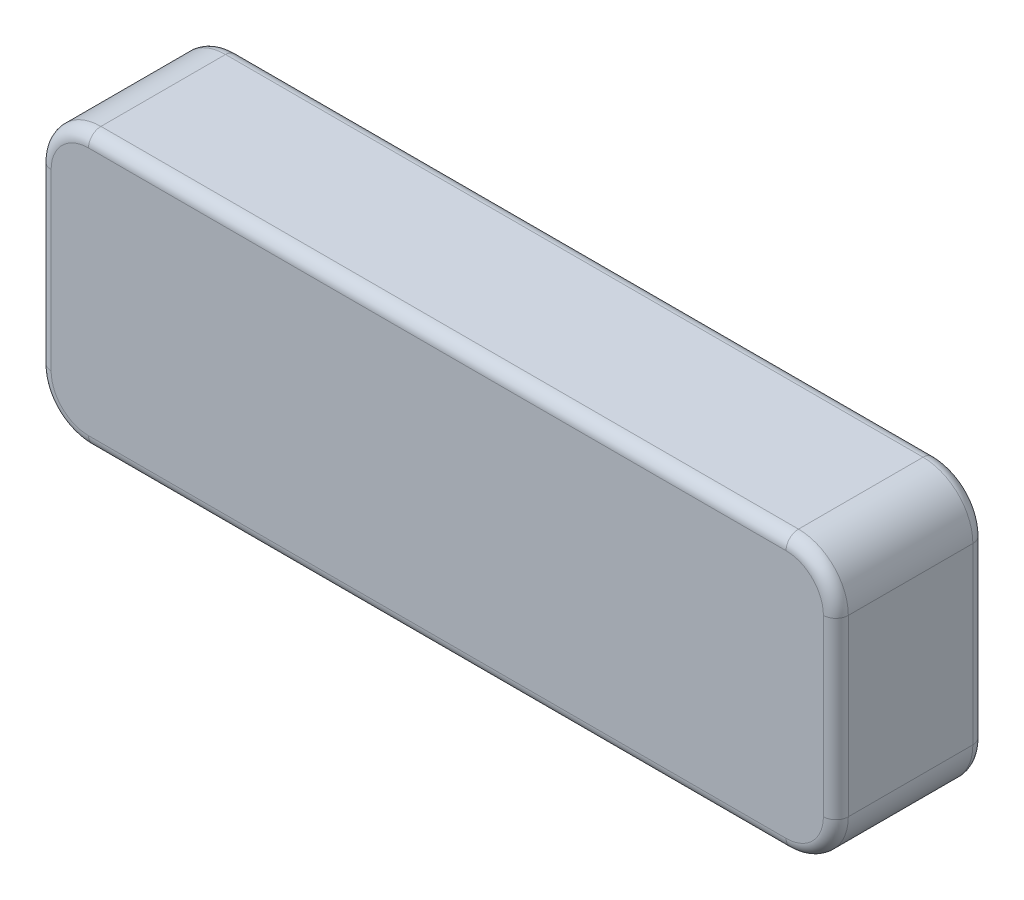
SolidWorks part; units mm, degrees
ref_plane "Front Plane" through (0, 0, 0) normal (0, 0, 1) x (1, 0, 0)
ref_plane "Top Plane" through (0, 0, 0) normal (0, 1, 0) x (1, 0, 0)
ref_plane "Right Plane" through (0, 0, 0) normal (1, 0, 0) x (0, 0, -1)
sketch "Sketch1" plane through (0, 0, 0) normal (0, 0, 1) x (1, 0, 0)
  line L1 (-203.2, -69.85) -> (203.2, -69.85)
  line L2 (-203.2, -69.85) -> (-203.2, 69.85)
  line L3 (-203.2, 69.85) -> (203.2, 69.85)
  line L4 (203.2, -69.85) -> (203.2, 69.85)
  line L5 (-203.2, -69.85) -> (203.2, 69.85) construction
  line L6 (-203.2, 69.85) -> (203.2, -69.85) construction
  point P0 (0, 0)
  dimension "D1" = 406.4
  dimension "D2" = 139.7
extrude "Boss-Extrude1" add sketch "Sketch1" along normal blind 76.2
fillet "Fillet1" radius 25.4 4 edges at (203.2, -69.85, 38.1) (-203.2, -69.85, 38.1) (-203.2, 69.85, 38.1) (203.2, 69.85, 38.1)
fillet "Fillet2" radius 6.35 16 edges at (195.7605, 62.4105, 0) (203.2, 0, 0) (195.7605, -62.4105, 0) (0, -69.85, 0) (-195.7605, -62.4105, 0) (-203.2, 0, 0) (-195.7605, 62.4105, 0) (195.7605, 62.4105, 76.2) (203.2, 0, 76.2) (195.7605, -62.4105, 76.2) (0, -69.85, 76.2) (-195.7605, -62.4105, 76.2) (-203.2, 0, 76.2) (-195.7605, 62.4105, 76.2) (0, 69.85, 0) (0, 69.85, 76.2)
